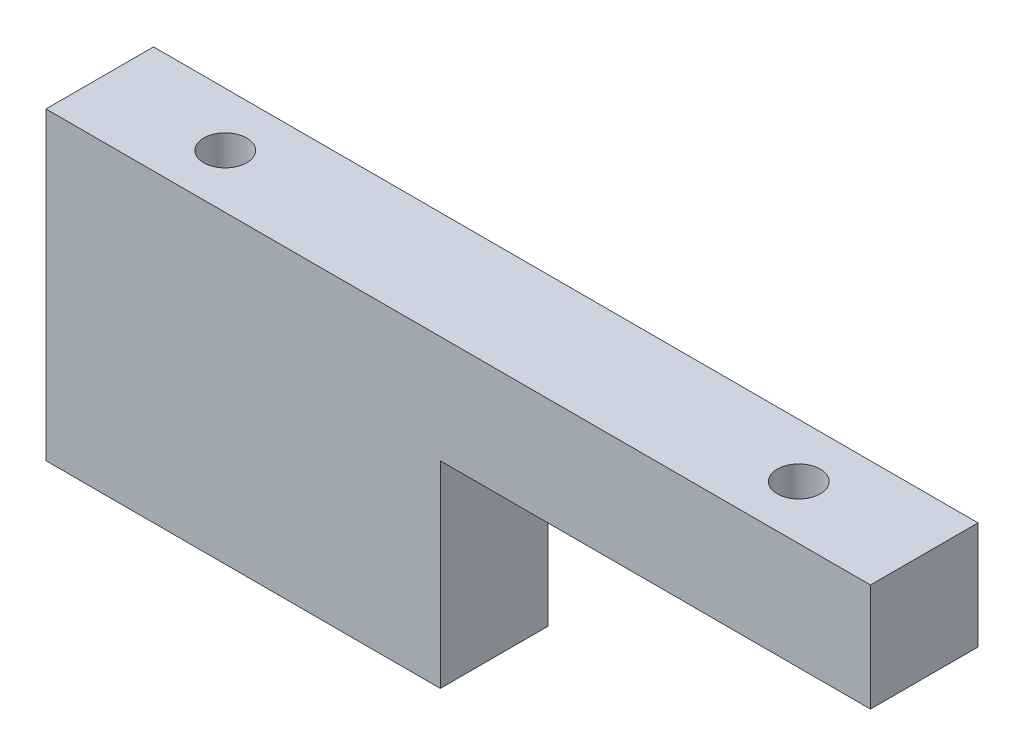
SolidWorks part; units mm, degrees
ref_plane "Front Plane" through (0, 0, 0) normal (0, 0, 1) x (1, 0, 0)
ref_plane "Top Plane" through (0, 0, 0) normal (0, 1, 0) x (1, 0, 0)
ref_plane "Right Plane" through (0, 0, 0) normal (1, 0, 0) x (0, 0, -1)
sketch "Sketch1" plane through (0, 0, 0) normal (0, 1, 0) x (1, 0, 0)
  line L1 (-57.5, -7.5) -> (57.5, -7.5)
  line L2 (-57.5, -7.5) -> (-57.5, 7.5)
  line L3 (-57.5, 7.5) -> (57.5, 7.5)
  line L4 (57.5, -7.5) -> (57.5, 7.5)
  line L5 (-57.5, -7.5) -> (57.5, 7.5) construction
  line L6 (-57.5, 7.5) -> (57.5, -7.5) construction
  point P0 (0, 0)
  dimension "D1" = 15
  dimension "D2" = 115
extrude "Boss-Extrude1" add sketch "Sketch1" along normal blind 42.5
sketch "Sketch2" plane through (0, 42.5, 0) normal (0, 1, 0) x (1, 0, 0)
  line L0 (-40, 0) -> (40, 0) construction
  circle A0 centre (-40, 0) radius 3
  circle A1 centre (40, 0) radius 3
  dimension "D2" = 6
  dimension "D1" = 80
extrude "Cut-Extrude1" cut sketch "Sketch2" against normal blind 42.5
sketch "Sketch3" plane through (0, 0, 7.5) normal (0, 0, 1) x (1, 0, 0)
  line L0 (-57.5, 42.5) -> (57.5, 42.5) construction
  line L1 (57.5, 0) -> (-2.5, 0)
  line L2 (57.5, 0) -> (57.5, 27.5)
  line L3 (57.5, 27.5) -> (-2.5, 27.5)
  line L4 (-2.5, 0) -> (-2.5, 27.5)
  dimension "D1" = 60
  dimension "D2" = 15
extrude "Cut-Extrude2" cut sketch "Sketch3" against normal up to next and the other way through all
